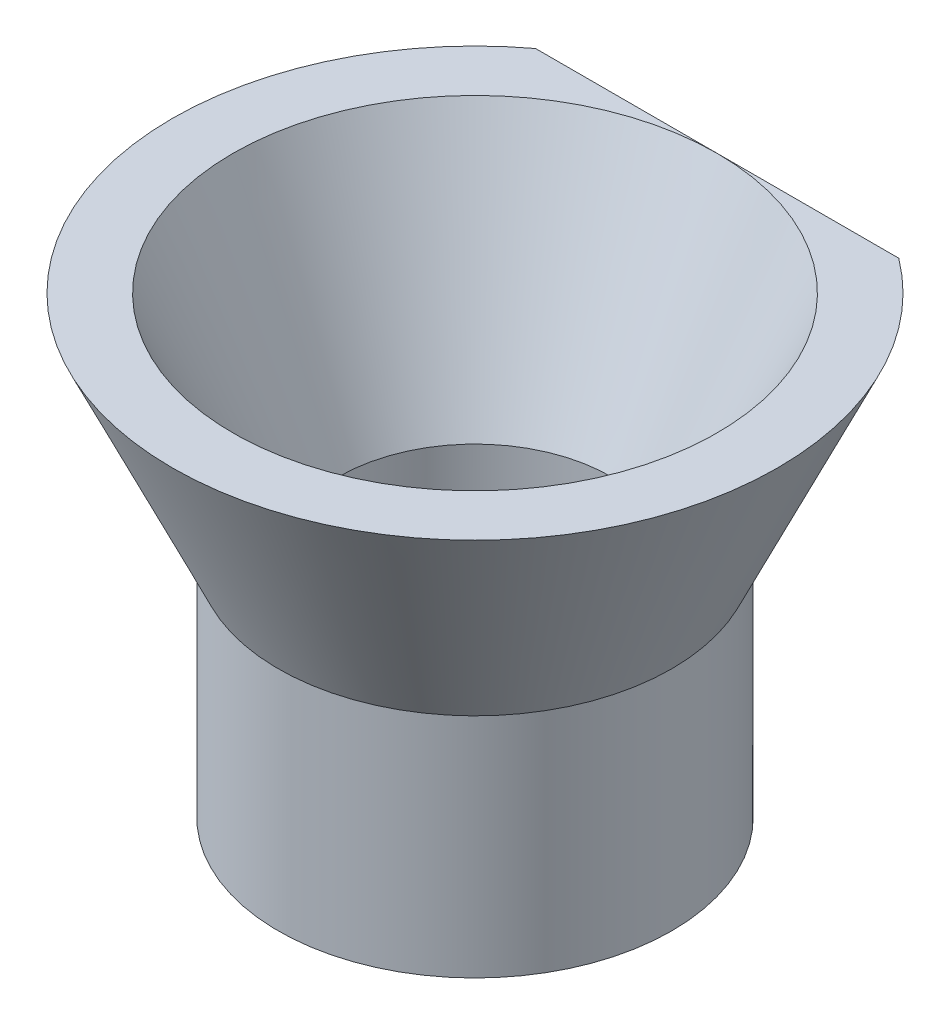
SolidWorks part; units mm, degrees
ref_plane "Alzado" through (0, 0, 0) normal (0, 0, 1) x (1, 0, 0)
ref_plane "Planta" through (0, 0, 0) normal (0, 1, 0) x (1, 0, 0)
ref_plane "Vista lateral" through (0, 0, 0) normal (1, 0, 0) x (0, 0, -1)
sketch "Croquis2" plane through (0, 0, 0) normal (0, 0, 1) x (1, 0, 0)
  line L0 (0, 0) -> (-4.5, 0) construction
  line L1 (-4.5, 0) -> (-8, 7.5)
  line L2 (-8, 7.5) -> (0, 7.5) construction
  line L3 (0, 7.5) -> (0, 0) construction
  line L4 (-8, 7.5) -> (-10, 7.5)
  line L5 (-10, 7.5) -> (-6.5, 0)
  line L6 (-6.5, 0) -> (-4.5, 0)
  dimension "D1" = 7.5
  dimension "D2" = 8
  dimension "D3" = 4.5
  dimension "D4" = 2
  dimension "D5" = 2
revolve "Revolución1" add sketch "Croquis2" angle 360 about L3
sketch "Croquis3" plane through (0, 0, 0) normal (0, -1, 0) x (1, 0, 0)
  circle A0 centre (0, 0) radius 4.5
  circle A1 centre (0, 0) radius 6.5
  dimension "D1" = 9
  dimension "D2" = 2
extrude "Saliente-Extruir1" add sketch "Croquis3" along normal blind 7.5
sketch "Croquis4" plane through (0, 7.5, 0) normal (0, 1, 0) x (1, 0, 0)
  line L0 (-9.0278, 8) -> (9.0278, 8)
  line L1 (9.0278, 8) -> (9.0278, 15.3566)
  line L2 (9.0278, 15.3566) -> (-9.4671, 15.3566)
  line L3 (-9.4671, 15.3566) -> (-9.0278, 8)
  point P3 (0, 8)
extrude "Cortar-Extruir1" cut sketch "Croquis4" against normal blind 7.5
